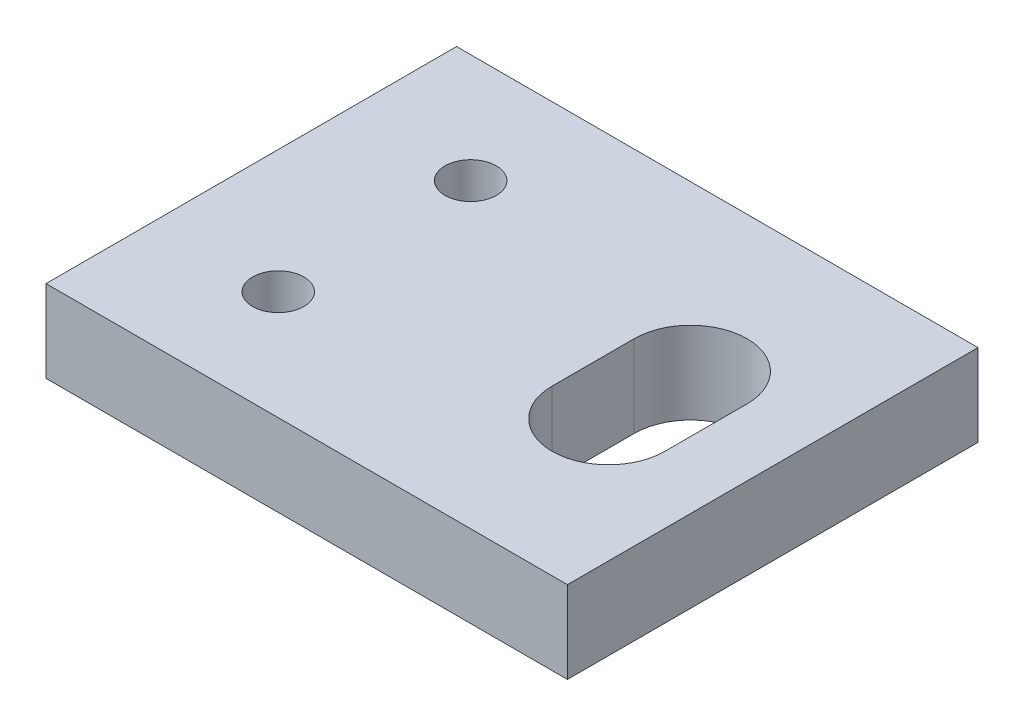
SolidWorks part; units mm, degrees
material "ABS"
ref_plane "Front Plane" through (0, 0, 0) normal (0, 0, 1) x (1, 0, 0)
ref_plane "Top Plane" through (0, 0, 0) normal (0, 1, 0) x (1, 0, 0)
ref_plane "Right Plane" through (0, 0, 0) normal (1, 0, 0) x (0, 0, -1)
ref_plane "Plane1" through (0, 4, 0) normal (0, 1, 0) x (1, 0, 0)
sketch "Sketch1" plane through (0, 4, 0) normal (0, 1, 0) x (1, 0, 0)
  line L0 (0, -10) -> (25.4, -10) construction
  line L2 (0, -20) -> (25.4, -20)
  line L3 (25.4, -20) -> (25.4, 0)
  line L4 (25.4, 0) -> (0, 0)
  line L5 (0, 0) -> (0, -20)
  line L6 (19.4, -12) -> (19.4, -8) construction
  line L7 (16.65, -12) -> (16.65, -8)
  line L8 (22.15, -12) -> (22.15, -8)
  circle A0 centre (6, -14.686) radius 1.25
  circle A3 centre (6, -5.314) radius 1.25
  arc A4 (16.65, -12) -> (22.15, -12) centre (19.4, -12) ccw
  arc A5 (22.15, -8) -> (16.65, -8) centre (19.4, -8) ccw
  point P16 (19.4, -10)
  dimension "D1" = 25.4
  dimension "D2" = 2.75
  dimension "D5" = 2.5
  dimension "D3" = 20
  dimension "D4" = 4
  dimension "D6" = 6
  dimension "D7" = 6
  dimension "D8" = 9.372
  dimension "D10" = 10
extrude "Boss-Extrude1" add sketch "Sketch1" against normal blind 4
